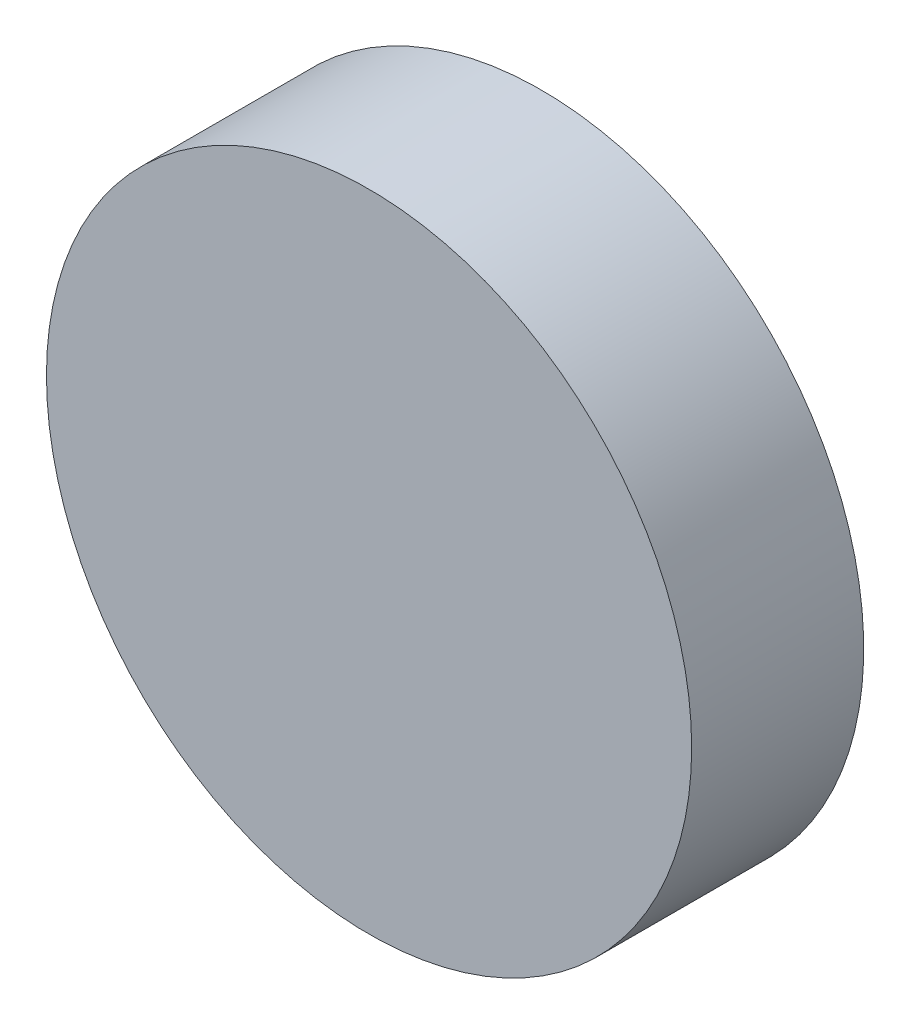
SolidWorks part; units mm, degrees
ref_plane "Alzado" through (0, 0, 0) normal (0, 0, 1) x (1, 0, 0)
ref_plane "Planta" through (0, 0, 0) normal (0, 1, 0) x (1, 0, 0)
ref_plane "Vista lateral" through (0, 0, 0) normal (1, 0, 0) x (0, 0, -1)
sketch "Croquis1" plane through (0, 0, 0) normal (0, 0, 1) x (1, 0, 0)
  circle A0 centre (0, 0) radius 15
  dimension "D1" = 30
extrude "Saliente-Extruir3" add sketch "Croquis1" along normal blind 2
sketch "Croquis3" plane through (0, 0, 2) normal (0, 0, 1) x (1, 0, 0)
  circle A0 centre (0, 0) radius 7.5
  dimension "D1" = 15
extrude "Saliente-Extruir4" add sketch "Croquis3" along normal blind 4
sketch "Croquis4" plane through (0, 0, 0) normal (0, 0, -1) x (-1, 0, 0)
  circle A0 centre (0, 0) radius 15
extrude "Cortar-Extruir1" cut sketch "Croquis4" against normal blind 2
sketch "Croquis5" plane through (0, 0, 2) normal (0, 0, -1) x (-1, 0, 0)
  line L0 (0, -7.5) -> (0, 7.5) construction
  circle A0 centre (0, 0) radius 7.5 construction
  dimension "D1" = 15
